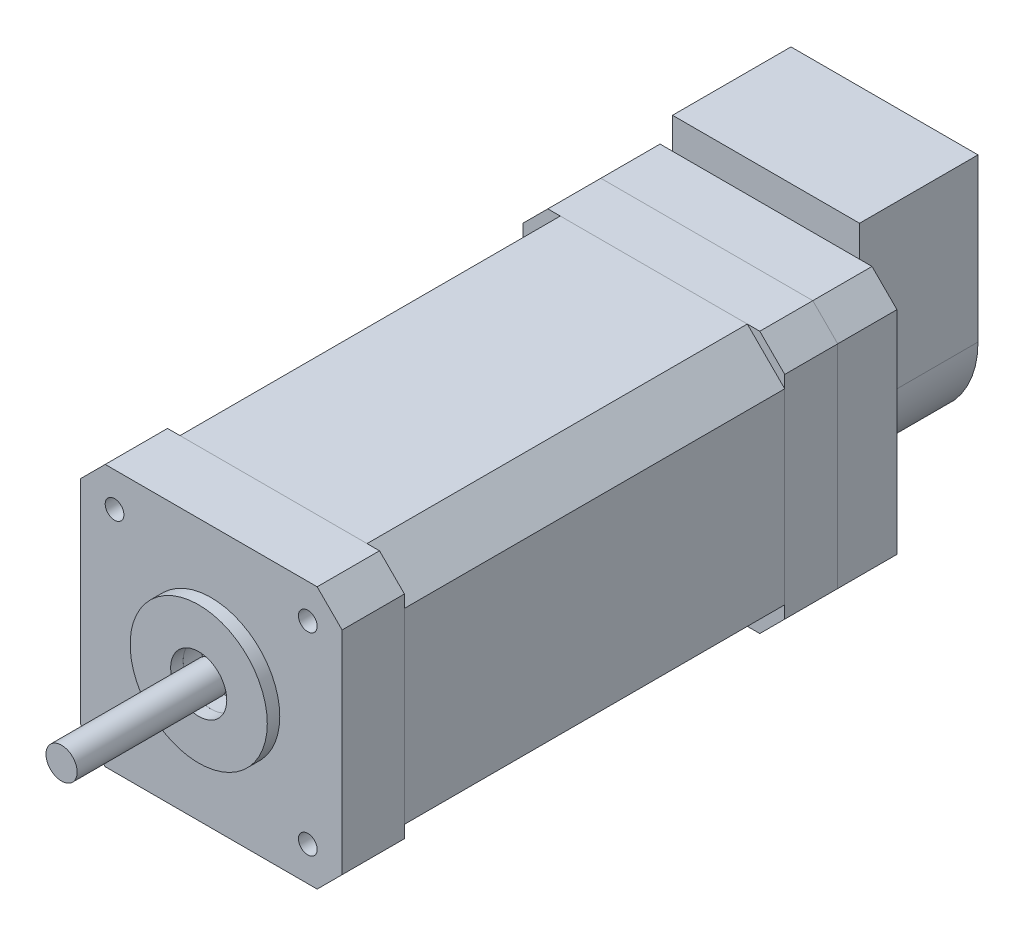
SolidWorks part; units mm, degrees
material "AISI 304"
ref_plane "前基準面" through (0, 0, 0) normal (0, 0, 1) x (1, 0, 0)
ref_plane "上基準面" through (0, 0, 0) normal (0, 1, 0) x (1, 0, 0)
ref_plane "右基準面" through (0, 0, 0) normal (1, 0, 0) x (0, 0, -1)
sketch "草圖1" plane through (0, 0, 0) normal (0, 0, 1) x (1, 0, 0)
  line L1 (-21, -21) -> (21, -21)
  line L2 (-21, -21) -> (-21, 21)
  line L3 (-21, 21) -> (21, 21)
  line L4 (21, -21) -> (21, 21)
  line L5 (-21, -21) -> (21, 21) construction
  line L6 (-21, 21) -> (21, -21) construction
  point P0 (0, 0)
  dimension "D1" = 42
  dimension "D2" = 42
extrude "填料-伸長1" add sketch "草圖1" along normal mid plane 61
chamfer "導角1" distance 6 angle 45 4 edges at (21, -21, 0) (-21, -21, 0) (-21, 21, 0) (21, 21, 0)
sketch "草圖15" plane through (0, 0, 30.5) normal (0, 0, 1) x (1, 0, 0)
  line L0 (15, 21) -> (-15, 21) construction
  line L1 (-21, -21) -> (21, -21)
  line L2 (-21, -21) -> (-21, 21)
  line L3 (-21, 21) -> (21, 21)
  line L4 (21, -21) -> (21, 21)
  line L5 (-21, -21) -> (21, 21) construction
  line L6 (-21, 21) -> (21, -21) construction
  line L7 (21, -15) -> (21, 15) construction
  point P0 (0, 0)
extrude "填料-伸長11" add sketch "草圖15" along normal blind 10 separate body
sketch "草圖16" plane through (0, 0, -30.5) normal (0, 0, -1) x (-1, 0, 0)
  line L1 (-21, -21) -> (21, -21)
  line L2 (-21, -21) -> (-21, 21)
  line L3 (-21, 21) -> (21, 21)
  line L4 (21, -21) -> (21, 21)
  line L5 (-21, -21) -> (21, 21) construction
  line L6 (-21, 21) -> (21, -21) construction
  line L8 (-15, 21) -> (15, 21) construction
  line L9 (21, 15) -> (21, -15) construction
  point P0 (0, 0)
extrude "填料-伸長12" add sketch "草圖16" along normal blind 8.5 separate body
sketch "草圖17" plane through (0, 0, -39) normal (0, 0, 1) x (1, 0, 0)
  line L0 (-21, 21) -> (21, 21) construction
  line L1 (-21, -21) -> (21, -21)
  line L2 (-21, -21) -> (-21, 21)
  line L3 (-21, 21) -> (21, 21)
  line L4 (21, -21) -> (21, 21)
  line L5 (-21, -21) -> (21, 21) construction
  line L6 (-21, 21) -> (21, -21) construction
  line L7 (21, 21) -> (21, -21) construction
  point P0 (0, 0)
extrude "填料-伸長13" add sketch "草圖17" against normal blind 9.5 separate body
chamfer "導角2" distance 4 angle 45 4 edges at (-21, -21, 35.5) (21, -21, 35.5) (21, 21, 35.5) (-21, 21, 35.5)
chamfer "導角3" distance 4 angle 45 4 edges at (-21, -21, -34.75) (21, -21, -34.75) (-21, 21, -34.75) (21, 21, -34.75)
chamfer "導角4" distance 4 angle 45 4 edges at (21, 21, -43.75) (-21, 21, -43.75) (-21, -21, -43.75) (21, -21, -43.75)
sketch "草圖2" plane through (0, 0, 40.5) normal (0, 0, 1) x (1, 0, 0)
  circle A0 centre (0, 0) radius 11
  dimension "D1" = 22
extrude "填料-伸長2" add sketch "草圖2" along normal blind 2
sketch "草圖3" plane through (0, 0, 42.5) normal (0, 0, 1) x (1, 0, 0)
  circle A0 centre (0, 0) radius 4.5
  dimension "D1" = 9
extrude "除料-伸長1" cut sketch "草圖3" along direction (0, 0, -1) on the side against the normal blind 5
sketch "草圖6" plane through (0, 0, 40.5) normal (0, 0, 1) x (1, 0, 0)
  circle A0 centre (0, 0) radius 2.5
  dimension "D1" = 5
extrude "填料-伸長9" add sketch "草圖6" along direction (0, 0, 1) on the side of the normal offset from surface (24 mm away) 22 separate body
sketch "草圖9" plane through (0, 0, -48.5) normal (0, 0, -1) x (-1, 0, 0)
  line L0 (-15, 0) -> (-15, 26)
  line L1 (-15, 26) -> (15, 26)
  line L2 (15, 26) -> (15, 0)
  arc A0 (15, 0) -> (-15, 0) centre (0, 0) cw
  point P6 (0, -15)
  dimension "D1" = 15
  dimension "D2" = 41
extrude "填料-伸長10" add sketch "草圖9" along normal blind 19 separate body
sketch "草圖8" plane through (0, 0, 40.5) normal (0, 0, 1) x (1, 0, 0)
  line L0 (0, 0) -> (0, 15.5) construction
  line L1 (0, 15.5) -> (-15.5, 15.5) construction
  circle A0 centre (-15.5, 15.5) radius 1.5
  dimension "D3" = 3
  dimension "D1" = 15.5
  dimension "D2" = 15.5
extrude "除料-伸長3" cut sketch "草圖8" against normal blind 4.5
sketch "草圖11" plane through (0, 0, 64.5) normal (0, 0, 1) x (1, 0, 0)
  line L0 (-2, 1.5) -> (2, 1.5)
  circle A0 centre (0, 0) radius 2.5 construction
  arc A1 (2, 1.5) -> (-2, 1.5) centre (0, 0) ccw
  point P5 (0, 1.5)
  point P6 (0, 2.5)
  dimension "D1" = 1
extrude "除料-伸長4" [suppressed] cut sketch "草圖11" against normal blind 18
pattern_circular "環狀複製排列1" count 4 over 360 about axis through (0, 0, 0) along (0, 0, 1) of "除料-伸長3"
